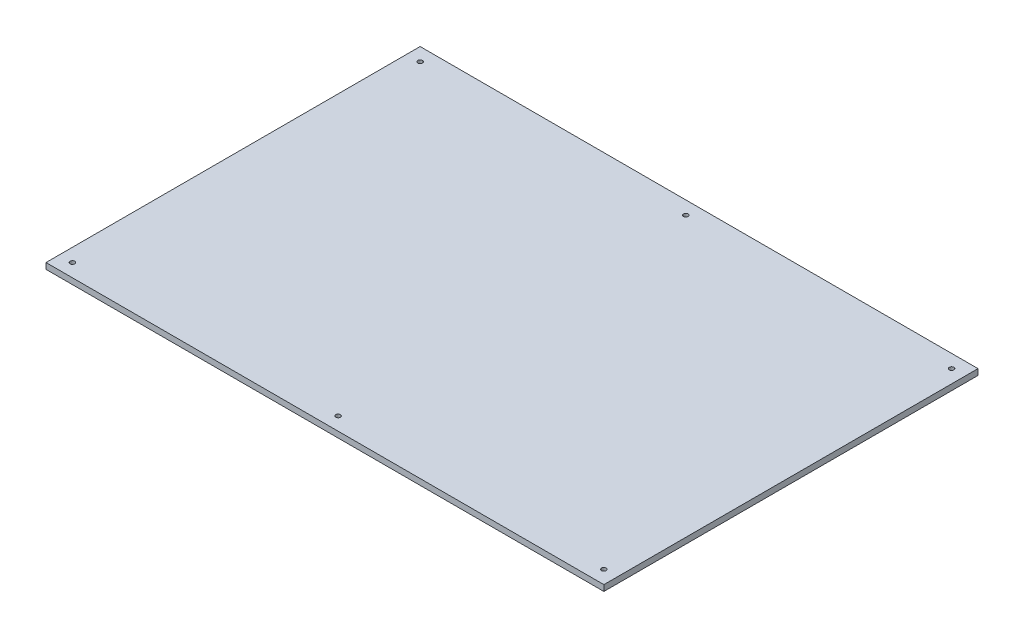
SolidWorks part; units mm, degrees
material "ABS"
ref_plane "Front Plane" through (0, 0, 0) normal (0, 0, 1) x (1, 0, 0)
ref_plane "Top Plane" through (0, 0, 0) normal (0, 1, 0) x (1, 0, 0)
ref_plane "Right Plane" through (0, 0, 0) normal (1, 0, 0) x (0, 0, -1)
sketch "Sketch1" plane through (0, 0, 0) normal (0, 1, 0) x (1, 0, 0)
  line L1 (211, -141.5) -> (-211, -141.5)
  line L2 (211, -141.5) -> (211, 141.5)
  line L3 (211, 141.5) -> (-211, 141.5)
  line L4 (-211, -141.5) -> (-211, 141.5)
  line L5 (211, -141.5) -> (-211, 141.5) construction
  line L6 (211, 141.5) -> (-211, -141.5) construction
  point P0 (0, 0)
  dimension "D1" = 422
  dimension "D2" = 283
extrude "Boss-Extrude1" add sketch "Sketch1" along normal blind 4.5
sketch "Sketch2" plane through (0, 4.5, 0) normal (0, 1, 0) x (1, 0, 0)
  line L0 (211, 141.5) -> (-211, 141.5) construction
  line L1 (-211, 141.5) -> (-211, -141.5) construction
  line L2 (0, 0) -> (0, 141.5) construction
  circle A0 centre (-201, 131.5) radius 1.75
  circle A1 centre (0, 131.5) radius 1.75
  dimension "D1" = 3.5
  dimension "D4" = 3.5
  dimension "D2" = 10
  dimension "D3" = 10
  dimension "D5" = 10
extrude "Cut-Extrude1" cut sketch "Sketch2" against normal up to next (4.5 mm away)
mirror "Mirror2" about plane through (0, 0, 0) normal (1, 0, 0) of "Cut-Extrude1"
mirror "Mirror3" about plane through (0, 0, 0) normal (0, 0, 1) of "Mirror2", "Cut-Extrude1"
